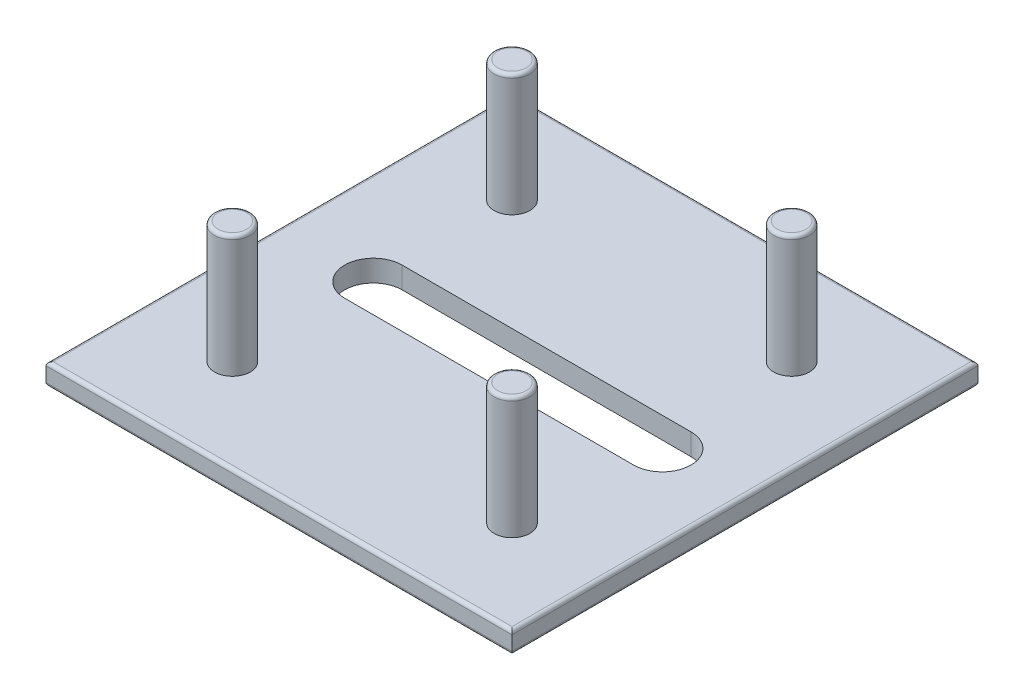
SolidWorks part; units mm, degrees
ref_plane "Alzado" through (0, 0, 0) normal (0, 0, 1) x (1, 0, 0)
ref_plane "Planta" through (0, 0, 0) normal (0, 1, 0) x (1, 0, 0)
ref_plane "Vista lateral" through (0, 0, 0) normal (1, 0, 0) x (0, 0, -1)
sketch "Sketch1" plane through (0, 0, 0) normal (0, 1, 0) x (1, 0, 0)
  line L1 (-32.5, 32.5) -> (32.5, 32.5)
  line L2 (-32.5, 32.5) -> (-32.5, -32.5)
  line L3 (-32.5, -32.5) -> (32.5, -32.5)
  line L4 (32.5, 32.5) -> (32.5, -32.5)
  line L5 (-32.5, 32.5) -> (32.5, -32.5) construction
  line L6 (-32.5, -32.5) -> (32.5, 32.5) construction
  point P0 (0, 0)
  dimension "D1" = 65
  dimension "D2" = 65
extrude "Boss-Extrude1" add sketch "Sketch1" along normal blind 3
sketch "Sketch2" plane through (0, 3, 0) normal (0, 1, 0) x (1, 0, 0)
  line L0 (-32.5, 32.5) -> (-32.5, -32.5) construction
  line L1 (32.5, 32.5) -> (-32.5, 32.5) construction
  line L2 (32.5, -32.5) -> (32.5, 32.5) construction
  line L3 (-32.5, -32.5) -> (32.5, -32.5) construction
  circle A0 centre (-19.5, 19.5) radius 2.5
  circle A1 centre (19.5, 19.5) radius 2.5
  circle A2 centre (-19.5, -19.5) radius 2.5
  circle A3 centre (19.5, -19.5) radius 2.5
  dimension "D1" = 5
  dimension "D4" = 13
  dimension "D2" = 13
  dimension "D3" = 13
  dimension "D5" = 13
  dimension "D6" = 13
  dimension "D7" = 13
  dimension "D8" = 13
extrude "Boss-Extrude2" add sketch "Sketch2" along normal blind 17
sketch "Sketch3" plane through (0, 0, 0) normal (0, -1, 0) x (1, 0, 0)
  line L0 (-32.5, 0) -> (32.5, 0) construction
  line L1 (-32.5, -32.5) -> (-32.5, 32.5) construction
  line L2 (32.5, 32.5) -> (32.5, -32.5) construction
  line L3 (-19.3358, 0) -> (20.9662, 0) construction
  line L4 (-19.3358, 4.0054) -> (20.9662, 4.0054)
  line L5 (-19.3358, -4.0054) -> (20.9662, -4.0054)
  arc A0 (-19.3358, 4.0054) -> (-19.3358, -4.0054) centre (-19.3358, 0) ccw
  arc A1 (20.9662, -4.0054) -> (20.9662, 4.0054) centre (20.9662, 0) ccw
  point P8 (0.8152, 0)
extrude "Cut-Extrude1" cut sketch "Sketch3" against normal through all
fillet "Fillet1" radius 0.5 12 edges at (19.5, 20, 22) (-19.5, 20, 22) (-19.5, 20, -17) (19.5, 20, -17) (32.5, 3, 0) (0, 3, -32.5) (0, 3, 32.5) (-32.5, 3, 0) (0, 0, -32.5) (32.5, 0, 0) (0, 0, 32.5) (-32.5, 0, 0)
